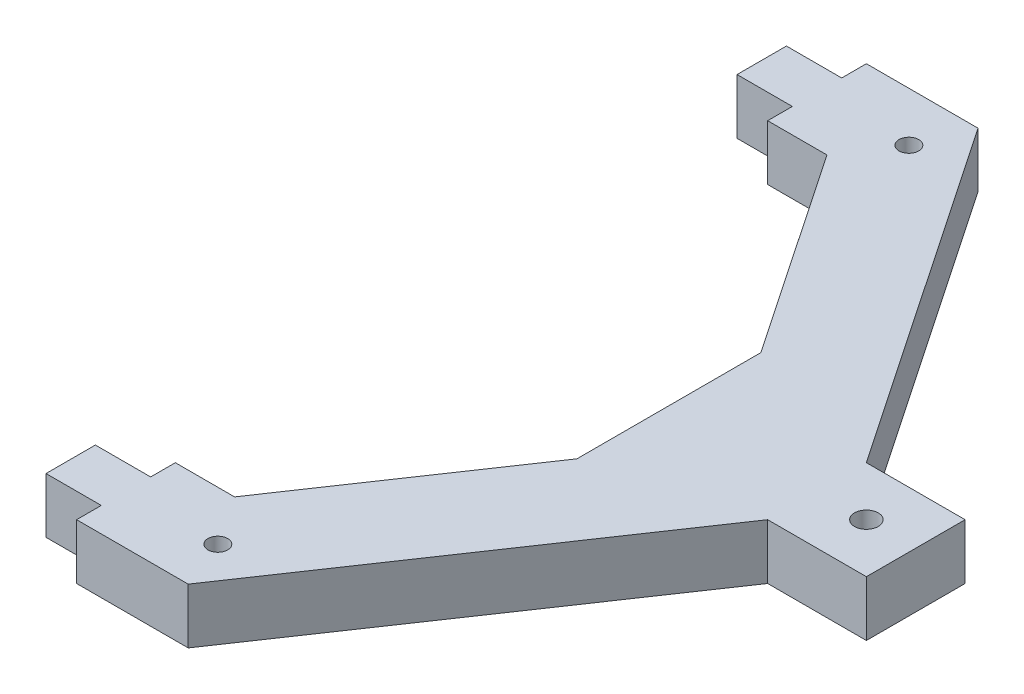
SolidWorks part; units mm, degrees
ref_plane "Front Plane" through (0, 0, 0) normal (0, 0, 1) x (1, 0, 0)
ref_plane "Top Plane" through (0, 0, 0) normal (0, 1, 0) x (1, 0, 0)
ref_plane "Right Plane" through (0, 0, 0) normal (1, 0, 0) x (0, 0, -1)
sketch "Sketch1" plane through (0, 0, 0) normal (0, 1, 0) x (1, 0, 0)
  line L0 (12.5, 25) -> (12.5, 0) construction
  line L1 (12.5, 0) -> (25, 0) construction
  line L2 (0, 12.5) -> (0, 25)
  line L3 (0, 25) -> (25, 25)
  line L4 (25, 12.5) -> (25, 25)
  line L5 (12.5, 0) -> (12.5, 12.5) construction
  line L6 (12.5, 12.5) -> (0, 12.5) construction
  line L7 (12.5, 12.5) -> (-87.5, 12.5) construction
  line L8 (0, 25) -> (-59.2343, 112.5)
  line L9 (-59.2343, 112.5) -> (-87.5, 112.5)
  line L10 (-87.5, 112.5) -> (-87.5, 87.5)
  line L11 (-87.5, 87.5) -> (-72.5, 87.5)
  line L12 (-72.5, 87.5) -> (-37.5, 35.7985)
  line L13 (-37.5, 35.7985) -> (-37.5, 12.5)
  line L14 (-37.5, 12.5) -> (0, 12.5)
  line L15 (0, 12.5) -> (0, 25)
  line L16 (-87.5, 87.5) -> (-87.5, 12.5) construction
  line L17 (0, 0) -> (12.5, 0) construction
  line L18 (0, 25) -> (25, 25)
  line L19 (0, 25) -> (0, 12.5)
  line L20 (0, 12.5) -> (25, 12.5)
  line L21 (25, 25) -> (25, 12.5)
  line L22 (25, 0) -> (25, 12.5) construction
  line L23 (0, 0) -> (0, 12.5) construction
  arc A0 (9.5, 12.5) -> (15.5, 12.5) centre (12.5, 12.5) cw
  dimension "D9" = 3
  dimension "D1" = 25
  dimension "D2" = 25
  dimension "D3" = 100
  dimension "D4" = 50
  dimension "D5" = 25
  dimension "D6" = 75
  dimension "D7" = 25
  dimension "D8" = 15
extrude "Boss-Extrude1" add sketch "Sketch1" along normal blind 14 contours L13 L14 L2 L8 L9 L10 L11 L12 | L2 L20 L4 L3
sketch "Sketch2" plane through (0, 14, 0) normal (0, 1, 0) x (1, 0, 0)
  line L0 (-87.5, 100) -> (-87.5, 112.5) construction
  line L1 (-101.5, 106.25) -> (-87.5, 106.25)
  line L2 (-101.5, 106.25) -> (-101.5, 93.75)
  line L3 (-101.5, 93.75) -> (-87.5, 93.75)
  line L4 (-87.5, 106.25) -> (-87.5, 93.75)
  line L5 (-87.5, 112.5) -> (-87.5, 87.5) construction
  point P9 (-87.5, 100)
  dimension "D1" = 12.5
  dimension "D2" = 14
extrude "Boss-Extrude2" add sketch "Sketch2" against normal up to surface (14 mm away) up to face at (-27.8849, 0, -48.9817)
mirror "Mirror1" about plane through (0, 14, -12.5) normal (0, 0, -1) of bodies 102
sketch "Sketch3" plane through (0, 14, 0) normal (0, 1, 0) x (1, 0, 0)
  line L0 (-59.2343, -87.5) -> (-87.5, -87.5) construction
  line L1 (-59.2343, 112.5) -> (-87.5, 112.5) construction
  point P0 (-64.2343, 100)
  point P1 (-64.2343, -75)
  dimension "D1" = 5
  dimension "D2" = 12.5
  dimension "D3" = 12.5
  dimension "D4" = 5
hole_wizard "Hole1" positions "Sketch4" profile "Sketch5" legacy end condition through all
sketch "Sketch4" plane through (0, 14, 0) normal (0, 1, 0) x (1, 0, 0)
  point P0 (-64.2343, 100)
  point P3 (-64.2343, -75)
sketch "Sketch5" plane through (-64.2343, 14, -100) normal (1, 0, 0) x (0, 0, 1)
  line L0 (0, 0) -> (0, 14)
  line L1 (0, 14) -> (2.5, 14)
  line L2 (2.5, 14) -> (2.5, 0)
  line L3 (2.5, 0) -> (0, 0)
  line L4 (0, 110) -> (0, -10) construction
  dimension "Diameter" = 5
  dimension "Depth" = 14
equation "\"ply\"= 14mm"
equation "\"D1@Boss-Extrude1\"=\"ply\""
equation "\"D2@Sketch2\"=\"ply\""
